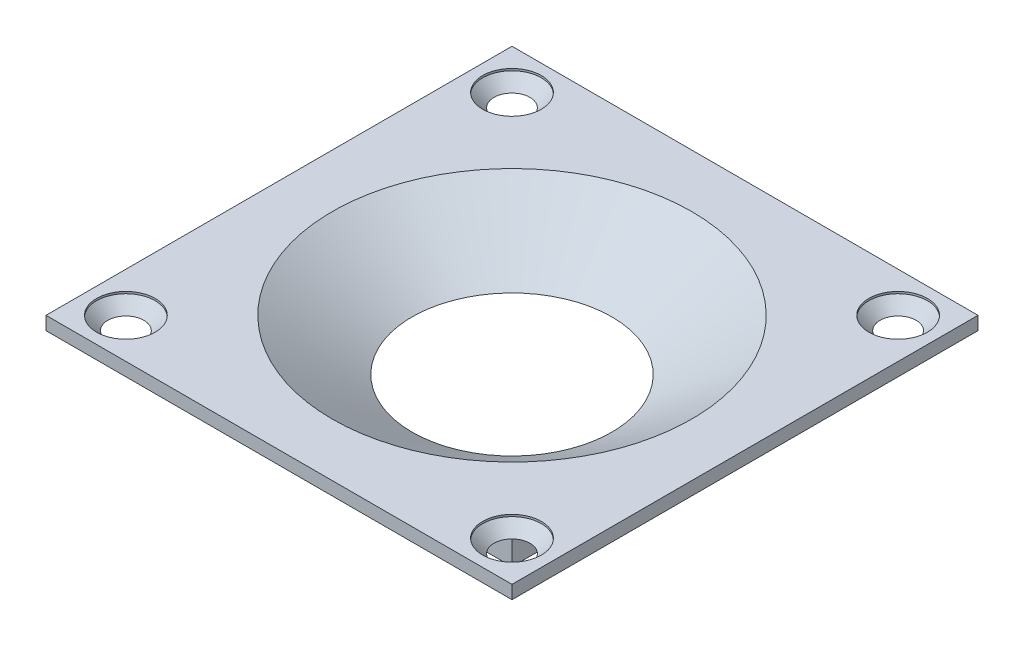
SolidWorks part; units mm, degrees
ref_plane "Front Plane" through (0, 0, 0) normal (0, 0, 1) x (1, 0, 0)
ref_plane "Top Plane" through (0, 0, 0) normal (0, 1, 0) x (1, 0, 0)
ref_plane "Right Plane" through (0, 0, 0) normal (1, 0, 0) x (0, 0, -1)
sketch "Sketch1" plane through (0, 0, 0) normal (0, 1, 0) x (1, 0, 0)
  line L1 (-12.5, -12.5) -> (12.5, -12.5)
  line L2 (-12.5, -12.5) -> (-12.5, 12.5)
  line L3 (-12.5, 12.5) -> (12.5, 12.5)
  line L4 (12.5, -12.5) -> (12.5, 12.5)
  line L5 (-12.5, -12.5) -> (12.5, 12.5) construction
  line L6 (-12.5, 12.5) -> (12.5, -12.5) construction
  point P0 (0, 0)
  dimension "D1" = 25
extrude "Boss-Extrude1" add sketch "Sketch1" along normal blind 2.85
sketch "Sketch2" plane through (0, 2.85, 0) normal (0, 1, 0) x (1, 0, 0)
  line L0 (12.5, -12.5) -> (12.5, 12.5) construction
  line L1 (-17.5, -17.5) -> (17.5, -17.5)
  line L2 (-17.5, -17.5) -> (-17.5, 17.5)
  line L3 (-17.5, 17.5) -> (17.5, 17.5)
  line L4 (17.5, -17.5) -> (17.5, 17.5)
  line L5 (-17.5, -17.5) -> (17.5, 17.5) construction
  line L6 (-17.5, 17.5) -> (17.5, -17.5) construction
  line L7 (12.5, 12.5) -> (-12.5, 12.5) construction
  point P0 (0, 0)
  dimension "D1" = 5
  dimension "D2" = 5
extrude "Boss-Extrude2" add sketch "Sketch2" along normal blind 1
sketch "Sketch3" plane through (0, 0, 0) normal (0, 0, 1) x (1, 0, 0)
  line L0 (0, 0) -> (0, 12.7105) construction
  line L1 (-12.5, 0) -> (12.5, 0) construction
  line L2 (0, 0) -> (7.5, 0)
  line L3 (7.5, 0) -> (13.5, 3.85)
  line L4 (-17.5, 3.85) -> (17.5, 3.85) construction
  line L5 (13.5, 3.85) -> (0, 3.85)
  line L6 (0, 3.85) -> (0, 0)
  dimension "D1" = 15
  dimension "D2" = 27
revolve "Cut-Revolve1" cut sketch "Sketch3" angle 360 about L0
hole_wizard "CSK for M2 Flat Head Machine Screw1" positions "Sketch5" profile "Sketch4" countersink size "M2" standard "ANSI Metric"
sketch "Sketch5" plane through (0, 3.85, 0) normal (0, 1, 0) x (1, 0, 0)
  line L0 (-14.5, -14.5) -> (-14.5, 14.5) construction
  line L1 (-14.5, 14.5) -> (14.5, 14.5) construction
  line L2 (14.5, 14.5) -> (14.5, -14.5) construction
  line L3 (14.5, -14.5) -> (-14.5, -14.5) construction
  line L5 (0, 14.5) -> (0, 0) construction
  line L6 (0, 0) -> (14.5, 0) construction
  point P0 (-14.5, 14.5)
  point P2 (14.5, 14.5)
  point P4 (14.5, -14.5)
  point P6 (-14.5, -14.5)
  dimension "D1" = 29
sketch "Sketch4" plane through (-14.5, 3.85, -14.5) normal (1, 0, 0) x (0, 0, 1)
  line L0 (0, 0) -> (0, 10.721)
  line L1 (0, 10.721) -> (1.2, 10)
  line L2 (1.2, 10) -> (1.2, 1.15)
  line L3 (1.2, 1.15) -> (2.2, 0.15)
  line L4 (2.2, 0.15) -> (2.2, 0)
  line L6 (2.2, 0) -> (0, 0)
  line L7 (-1.2, 1.15) -> (-2.2, 0.15) construction
  line L10 (0, 10.721) -> (-1.2, 10) construction
  line L11 (0, -6.35) -> (0, 107.95) construction
  dimension "Hole Dia." = 2.4
  dimension "Hole Depth" = 10
  dimension "C'Sink Dia." = 4.4
  dimension "C'Sink Angle" = 90
  dimension "Drill Angle" = 118
  dimension "Head Clearance" = 0.15
